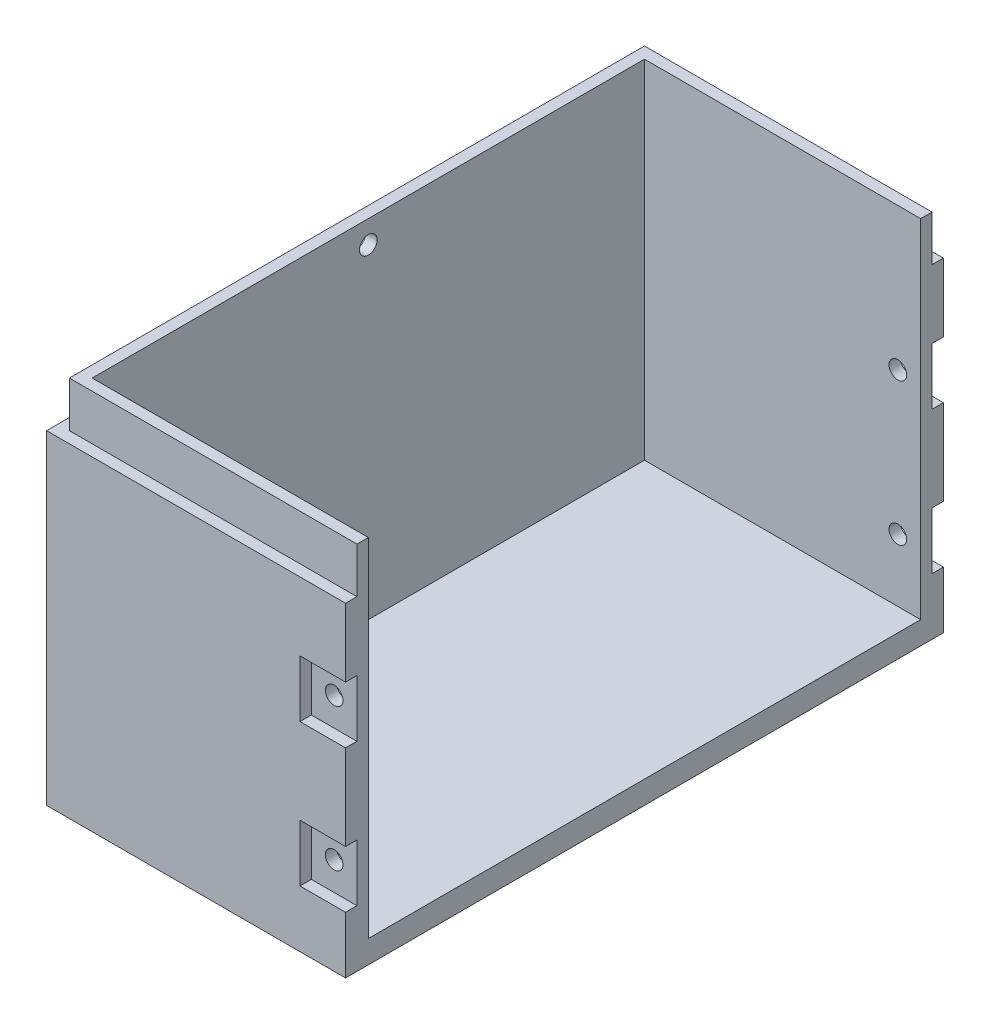
SolidWorks part; units mm, degrees
ref_plane "Front Plane" through (0, 0, 0) normal (0, 0, 1) x (1, 0, 0)
ref_plane "Top Plane" through (0, 0, 0) normal (0, 1, 0) x (1, 0, 0)
ref_plane "Right Plane" through (0, 0, 0) normal (1, 0, 0) x (0, 0, -1)
sketch "Sketch1" plane through (0, 0, 0) normal (0, 1, 0) x (1, 0, 0)
  line L1 (-26.25, 52.5) -> (26.25, 52.5)
  line L2 (-26.25, 52.5) -> (-26.25, -52.5)
  line L3 (-26.25, -52.5) -> (26.25, -52.5)
  line L4 (26.25, 52.5) -> (26.25, -52.5)
  line L5 (-26.25, 52.5) -> (26.25, -52.5) construction
  line L6 (-26.25, -52.5) -> (26.25, 52.5) construction
  point P0 (0, 0)
  dimension "D1" = 52.5
  dimension "D2" = 105
extrude "Boss-Extrude1" add sketch "Sketch1" along normal blind 65
sketch "Sketch2" plane through (26.25, 0, 0) normal (1, 0, 0) x (0, 0, -1)
  line L0 (-52.5, 65) -> (52.5, 65) construction
  line L1 (-48.5, 65) -> (48.5, 65)
  line L2 (-48.5, 65) -> (-48.5, 4)
  line L3 (-48.5, 4) -> (48.5, 4)
  line L4 (48.5, 65) -> (48.5, 4)
  line L5 (-52.5, 65) -> (-52.5, 0) construction
  line L6 (52.5, 65) -> (52.5, 0) construction
  line L7 (-52.5, 0) -> (52.5, 0) construction
  dimension "D1" = 4
  dimension "D2" = 4
  dimension "D3" = 4
extrude "Cut-Extrude1" cut sketch "Sketch2" against normal blind 48.5
sketch "Sketch4" plane through (0, 0, -52.5) normal (0, 0, -1) x (-1, 0, 0)
  line L0 (26.25, 65) -> (26.25, 0) construction
  line L1 (-26.25, 65) -> (26.25, 65)
  line L2 (-26.25, 65) -> (-26.25, 57)
  line L3 (-26.25, 57) -> (26.25, 57)
  line L4 (26.25, 65) -> (26.25, 57)
  line L5 (-26.25, 0) -> (26.25, 0) construction
  line L6 (-26.25, 57) -> (-18.25, 57)
  line L7 (-26.25, 57) -> (-26.25, 0)
  line L8 (-26.25, 0) -> (-18.25, 0)
  line L9 (-18.25, 57) -> (-18.25, 0)
  point P12 (-28.75, 57)
  line M1 (-26.25, 0) -> (26.25, 0)
  line M2 (26.25, 0) -> (26.25, 65)
  line M3 (26.25, 65) -> (-26.25, 65)
  line M4 (-26.25, 65) -> (-26.25, 0)
  dimension "D1" = 8
  dimension "D2" = 8
extrude "Cut-Extrude2" cut sketch "Sketch4" against normal blind 2 contours L9 L3 M4 M1 | L3 M4 M2 M3
sketch "Sketch5" plane through (0, 0, 52.5) normal (0, 0, 1) x (1, 0, 0)
  line L0 (-26.25, 65) -> (-26.25, 0) construction
  line L1 (26.25, 65) -> (-26.25, 65)
  line L2 (26.25, 65) -> (26.25, 57)
  line L3 (26.25, 57) -> (-26.25, 57)
  line L4 (-26.25, 65) -> (-26.25, 57)
  line L5 (-26.25, 0) -> (26.25, 0) construction
  line L6 (26.25, 57) -> (18.25, 57)
  line L7 (26.25, 57) -> (26.25, 0)
  line L8 (26.25, 0) -> (18.25, 0)
  line L9 (18.25, 57) -> (18.25, 0)
  line M1 (-26.25, 0) -> (26.25, 0)
  line M2 (26.25, 0) -> (26.25, 65)
  line M3 (26.25, 65) -> (-26.25, 65)
  line M4 (-26.25, 65) -> (-26.25, 0)
  dimension "D1" = 8
  dimension "D2" = 8
extrude "Cut-Extrude3" cut sketch "Sketch5" against normal blind 2 contours L3 M2 M3 M4 | L3 L9 M1 M2
sketch "Sketch7" plane through (-26.25, 0, 0) normal (-1, 0, 0) x (0, 0, 1)
  line L1 (-50.5, 65) -> (50.5, 65)
  line L2 (-50.5, 65) -> (-50.5, 57)
  line L3 (-50.5, 57) -> (50.5, 57)
  line L4 (50.5, 65) -> (50.5, 57)
extrude "Cut-Extrude5" cut sketch "Sketch7" against normal blind 2
sketch "Sketch9" plane through (-24.25, 0, 0) normal (-1, 0, 0) x (0, 0, 1)
  line L0 (50.5, 65) -> (-50.5, 65) construction
  circle A0 centre (0, 61) radius 1.55
  dimension "D1" = 3.1
  dimension "D2" = 4
extrude "Cut-Extrude6" cut sketch "Sketch9" against normal up to next
sketch "Sketch10" plane through (0, 0, 50.5) normal (0, 0, 1) x (1, 0, 0)
  line L0 (18.25, 0) -> (26.25, 0) construction
  line L1 (26.25, 0) -> (26.25, 65) construction
  circle A0 centre (22.25, 15) radius 1.55
  circle A1 centre (22.25, 40) radius 1.55
  dimension "D1" = 3.1
  dimension "D2" = 3.1
  dimension "D3" = 15
  dimension "D6" = 4
  dimension "D4" = 25
  dimension "D5" = 4
extrude "Cut-Extrude7" cut sketch "Sketch10" against normal through all
sketch "Sketch12" plane through (0, 0, 50.5) normal (0, 0, 1) x (1, 0, 0)
  line L0 (26.25, 0) -> (26.25, 65) construction
  line L1 (18.25, 57) -> (26.25, 57)
  line L2 (18.25, 57) -> (18.25, 45)
  line L3 (18.25, 45) -> (26.25, 45)
  line L4 (26.25, 57) -> (26.25, 45)
  line L5 (18.25, 0) -> (26.25, 0) construction
  line L6 (26.25, 0) -> (18.25, 0)
  line L7 (26.25, 0) -> (26.25, 10)
  line L8 (26.25, 10) -> (18.25, 10)
  line L9 (18.25, 0) -> (18.25, 10)
  line L10 (18.25, 57) -> (18.25, 0) construction
  line L11 (18.25, 57) -> (18.25, 0) construction
  line L12 (18.25, 35) -> (26.25, 35)
  line L13 (18.25, 35) -> (18.25, 20)
  line L14 (18.25, 20) -> (26.25, 20)
  line L15 (26.25, 35) -> (26.25, 20)
  circle A1 centre (22.25, 40) radius 1.55 construction
  circle A3 centre (22.25, 15) radius 1.55 construction
  dimension "D3" = 5
  dimension "D4" = 5
  dimension "D1" = 12
  dimension "D2" = 10
extrude "Boss-Extrude2" add sketch "Sketch12" along normal blind 2
sketch "Sketch13" plane through (0, 0, -50.5) normal (0, 0, -1) x (-1, 0, 0)
  line L0 (-26.25, 65) -> (-26.25, 0) construction
  line L1 (-18.25, 57) -> (-26.25, 57)
  line L2 (-18.25, 57) -> (-18.25, 45)
  line L3 (-18.25, 45) -> (-26.25, 45)
  line L4 (-26.25, 57) -> (-26.25, 45)
  line L5 (-18.25, 57) -> (-18.25, 0) construction
  line L6 (-26.25, 35) -> (-18.25, 35)
  line L7 (-26.25, 35) -> (-26.25, 20)
  line L8 (-26.25, 20) -> (-18.25, 20)
  line L9 (-18.25, 35) -> (-18.25, 20)
  line L11 (-18.25, 10) -> (-26.25, 10)
  line L12 (-18.25, 10) -> (-18.25, 0)
  line L13 (-18.25, 0) -> (-26.25, 0)
  line L14 (-26.25, 10) -> (-26.25, 0)
  circle A0 centre (-22.25, 40) radius 1.55 construction
  circle A1 centre (-22.25, 15) radius 1.55 construction
  dimension "D1" = 5
  dimension "D2" = 5
  dimension "D3" = 5
  dimension "D4" = 5
extrude "Boss-Extrude3" add sketch "Sketch13" along normal blind 2 contours L12 L11 L14 L13 | L2 L1 L4 L3 | L7 L6 L9 L8
